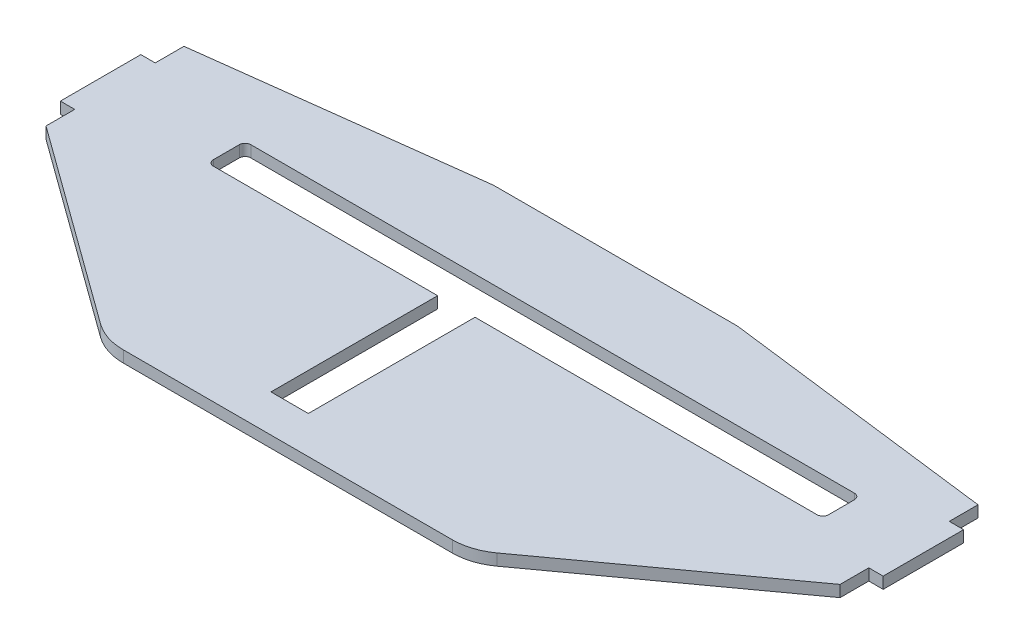
SolidWorks part; units mm, degrees
material "Fibra de Vidro S"
ref_plane "Plano frontal" through (0, 0, 0) normal (0, 0, 1) x (1, 0, 0)
ref_plane "Plano superior" through (0, 0, 0) normal (0, 1, 0) x (1, 0, 0)
ref_plane "Plano direito" through (0, 0, 0) normal (1, 0, 0) x (0, 0, -1)
sketch "Esboço1" plane through (0, 0, 0) normal (0, 1, 0) x (1, 0, 0)
  line L0 (-69.0672, 27.6905) -> (-21.8418, 33.6128)
  line L1 (-20.5975, 33.6905) -> (0, 33.6905)
  line L2 (0, -23.3095) -> (0, 33.6905)
  line L9 (0, -23.3095) -> (-28.6085, -23.3095)
  line L10 (-34.4811, -21.4035) -> (-69.0672, 3.6905)
  line L11 (-69.0672, 3.6905) -> (-69.0672, 8.6905)
  line L12 (-69.0672, 8.6905) -> (-71.5672, 8.6905)
  line L13 (-71.5672, 8.6905) -> (-71.5672, 22.6905)
  line L14 (-71.5672, 22.6905) -> (-69.0672, 22.6905)
  line L15 (-69.0672, 22.6905) -> (-69.0672, 27.6905)
  arc A0 (-20.5975, 33.6905) -> (-21.8418, 33.6128) centre (-20.5975, 23.6905) ccw
  arc A1 (-28.6085, -23.3095) -> (-34.4811, -21.4035) centre (-28.6085, -13.3095) cw
  point P6 (-21.2221, 33.6905)
  dimension "D1" = 10
  dimension "D2" = 6
  dimension "D3" = 57
  dimension "D4" = 2.5
  dimension "D5" = 24
  dimension "D7" = 5
extrude "Ressalto-extrusão1" add sketch "Esboço1" along normal blind 2
mirror "Espelhar1" about plane through (0, 2, 23.3095) normal (-1, 0, 0) of "Ressalto-extrusão1"
sketch "Esboço2" plane through (0, 2, 0) normal (0, 1, 0) x (1, 0, 0)
  line L0 (20.5975, 33.6905) -> (-20.5975, 33.6905) construction
  line L1 (-48.4328, 18.6905) -> (56.5672, 18.6905)
  line L2 (-49.4328, 17.6905) -> (-49.4328, 13.1905)
  line L3 (-48.4328, 12.1905) -> (-9.4328, 12.1905)
  line L4 (57.5672, 17.6905) -> (57.5672, 13.1905)
  line L5 (-49.4328, 18.6905) -> (57.5672, 12.1905) construction
  line L6 (-49.4328, 12.1905) -> (57.5672, 18.6905) construction
  line L7 (71.5672, 22.6905) -> (71.5672, 8.6905) construction
  line L8 (-2.9328, 12.1905) -> (56.5672, 12.1905)
  line L9 (-9.4328, -16.8095) -> (-2.9328, -16.8095)
  line L10 (-9.4328, -16.8095) -> (-9.4328, 12.1905)
  line L12 (-2.9328, -16.8095) -> (-2.9328, 12.1905)
  line L13 (-9.4328, -16.8095) -> (-2.9328, 12.1905) construction
  line L14 (-9.4328, 12.1905) -> (-2.9328, -16.8095) construction
  arc A0 (57.5672, 13.1905) -> (56.5672, 12.1905) centre (56.5672, 13.1905) cw
  arc A1 (57.5672, 17.6905) -> (56.5672, 18.6905) centre (56.5672, 17.6905) ccw
  arc A2 (-49.4328, 17.6905) -> (-48.4328, 18.6905) centre (-48.4328, 17.6905) cw
  arc A3 (-49.4328, 13.1905) -> (-48.4328, 12.1905) centre (-48.4328, 13.1905) ccw
  point P0 (4.0672, 15.4405)
  point P21 (-6.1828, -2.3095)
  dimension "D4" = 1
  dimension "D1" = 107
  dimension "D2" = 15
  dimension "D3" = 14
  dimension "D5" = 40
  dimension "D6" = 6.5
  dimension "D7" = 6.5
  dimension "D8" = 29
extrude "Corte-extrusão1" cut sketch "Esboço2" against normal through all
